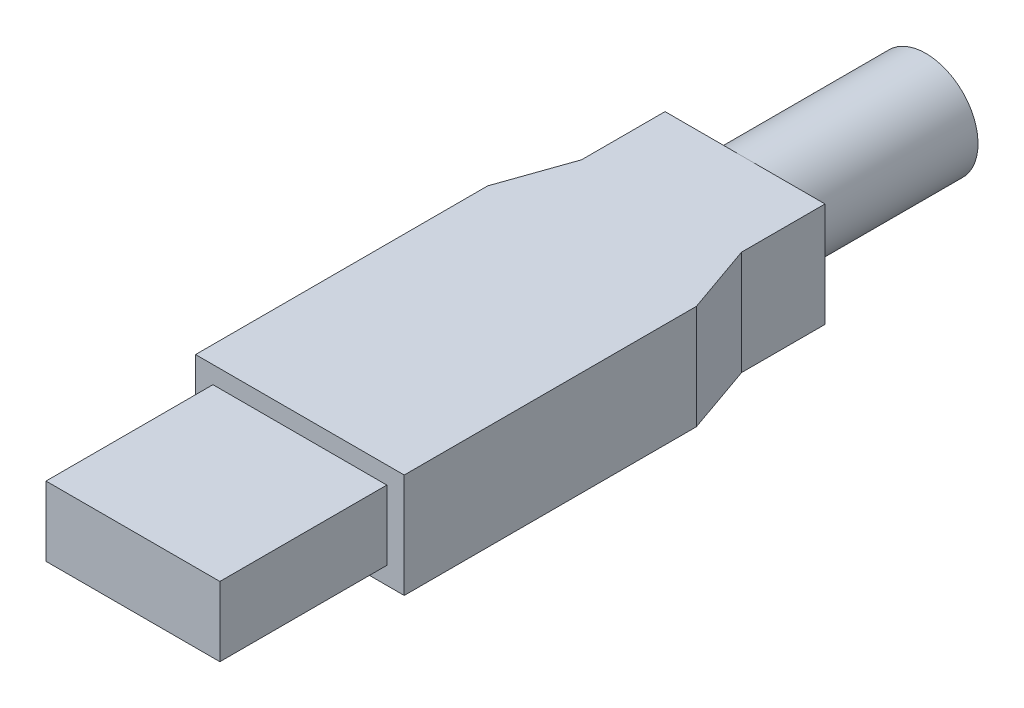
SolidWorks part; units mm, degrees
ref_plane "Vorne" through (0, 0, 0) normal (0, 0, 1) x (1, 0, 0)
ref_plane "Oben" through (0, 0, 0) normal (0, 1, 0) x (1, 0, 0)
ref_plane "Rechts" through (0, 0, 0) normal (1, 0, 0) x (0, 0, -1)
sketch "Skizze1" plane through (0, 0, 0) normal (0, 0, 1) x (1, 0, 0)
  line L0 (-6.25, 2.5) -> (0, 0) construction
  line L1 (-6.25, 2.5) -> (6.25, 2.5)
  line L2 (-6.25, 2.5) -> (-6.25, -2.5)
  line L3 (-6.25, -2.5) -> (6.25, -2.5)
  line L4 (6.25, 2.5) -> (6.25, -2.5)
  line L5 (0, 0) -> (6.25, -2.5) construction
  dimension "D1" = 12.5
  dimension "D2" = 5
extrude "Aufsatz-Linear austragen1" add sketch "Skizze1" along normal blind 12
sketch "Skizze2" plane through (0, 0, 0) normal (0, 0, -1) x (-1, 0, 0)
  line L0 (-7.5, 3.75) -> (0, 0) construction
  line L1 (-7.5, 3.75) -> (7.5, 3.75)
  line L2 (-7.5, 3.75) -> (-7.5, -3.75)
  line L3 (-7.5, -3.75) -> (7.5, -3.75)
  line L4 (7.5, 3.75) -> (7.5, -3.75)
  line L5 (0, 0) -> (7.5, -3.75) construction
  dimension "D1" = 15
  dimension "D2" = 7.5
extrude "Aufsatz-Linear austragen2" add sketch "Skizze2" along normal blind 21
sketch "Skizze3" plane through (0, 0, 0) normal (0, 1, 0) x (1, 0, 0)
  line L0 (-7.5, 21) -> (-5.75, 26)
  line L1 (-5.75, 26) -> (-5.75, 32)
  line L2 (-5.75, 32) -> (5.75, 32)
  line L3 (5.75, 32) -> (5.75, 26)
  line L4 (5.75, 26) -> (7.5, 21)
  line L5 (7.5, 21) -> (-7.5, 21)
  dimension "D1" = 11.5
  dimension "D2" = 6
  dimension "D3" = 11
extrude "Aufsatz-Linear austragen3" add sketch "Skizze3" along normal up to vertex (3.75 mm away) and the other way up to vertex (3.75 mm away)
sketch "Skizze4" plane through (0, 0, -32) normal (0, 0, -1) x (-1, 0, 0)
  line L0 (-5.75, 3.75) -> (5.75, 3.75) construction
  circle A0 centre (0, 0) radius 3.75
extrude "Aufsatz-Linear austragen4" add sketch "Skizze4" along normal blind 13
